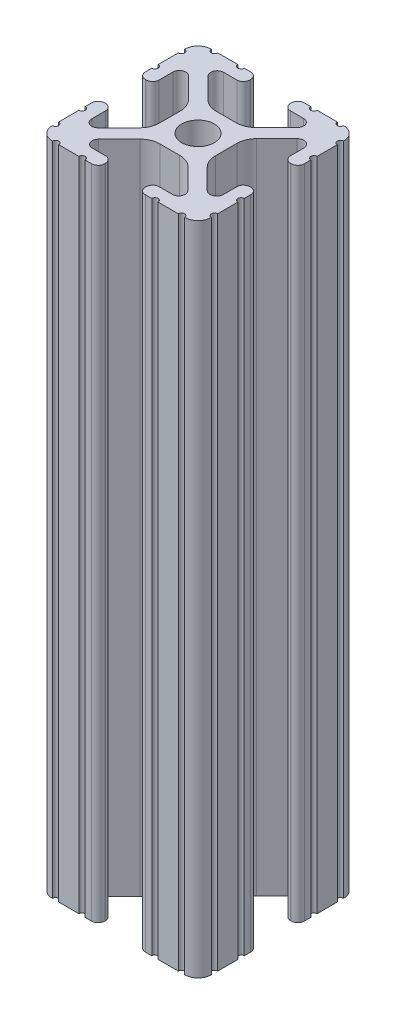
SolidWorks part; units mm, degrees
material "6061-T6 (SS)"
ref_plane "Front Plane" through (0, 0, 0) normal (0, 0, 1) x (1, 0, 0)
ref_plane "Top Plane" through (0, 0, 0) normal (0, 1, 0) x (1, 0, 0)
ref_plane "Right Plane" through (0, 0, 0) normal (1, 0, 0) x (0, 0, -1)
sketch "Sketch1" plane through (0, 0, 0) normal (0, 1, 0) x (0, 0, -1)
  line L0 (6.3331, -12.7) -> (9.5504, -12.7)
  line L1 (12.7, -9.5504) -> (12.7, -6.3331)
  line L2 (12.7, -5.3171) -> (12.7, -4.2875)
  line L3 (11.651, -3.2385) -> (11.5392, -3.2385)
  line L4 (10.4902, -4.2875) -> (10.4902, -6.4021)
  line L5 (8.7371, -7.1294) -> (5.441, -3.8408)
  line L6 (4.5085, -1.5932) -> (4.5085, 1.5932)
  line L7 (5.441, 3.8408) -> (8.7371, 7.1294)
  line L8 (10.4902, 6.4021) -> (10.4902, 4.2875)
  line L9 (11.5392, 3.2385) -> (11.651, 3.2385)
  line L10 (12.7, 4.2875) -> (12.7, 5.3171)
  line L11 (12.7, 6.3331) -> (12.7, 9.5504)
  line L12 (9.5504, 12.7) -> (6.3331, 12.7)
  line L13 (5.3171, 12.7) -> (4.2875, 12.7)
  line L14 (3.2385, 11.651) -> (3.2385, 11.5392)
  line L15 (4.2875, 10.4902) -> (6.4768, 10.4902)
  line L16 (7.207, 8.7244) -> (3.8983, 5.4232)
  line L17 (1.6558, 4.4958) -> (-1.6558, 4.4958)
  line L18 (-3.8983, 5.4232) -> (-7.207, 8.7244)
  line L19 (-6.4768, 10.4902) -> (-4.2875, 10.4902)
  line L20 (-3.2385, 11.5392) -> (-3.2385, 11.651)
  line L21 (-4.2875, 12.7) -> (-5.3171, 12.7)
  line L22 (-6.3331, 12.7) -> (-9.5504, 12.7)
  line L23 (-12.7, 9.5504) -> (-12.7, 6.3331)
  line L24 (-12.7, 5.3171) -> (-12.7, 4.2875)
  line L25 (-11.651, 3.2385) -> (-11.5392, 3.2385)
  line L26 (-10.4902, 4.2875) -> (-10.4902, 6.4021)
  line L27 (-8.7371, 7.1294) -> (-5.441, 3.8408)
  line L28 (-4.5085, 1.5932) -> (-4.5085, -1.5932)
  line L29 (-5.441, -3.8408) -> (-8.7371, -7.1294)
  line L30 (-10.4902, -6.4021) -> (-10.4902, -4.2875)
  line L31 (-11.5392, -3.2385) -> (-11.651, -3.2385)
  line L32 (-12.7, -4.2875) -> (-12.7, -5.3171)
  line L33 (-12.7, -6.3331) -> (-12.7, -9.5504)
  line L34 (-9.5504, -12.7) -> (-6.3331, -12.7)
  line L35 (-5.3171, -12.7) -> (-4.2875, -12.7)
  line L36 (-3.2385, -11.651) -> (-3.2385, -11.5392)
  line L37 (-4.2875, -10.4902) -> (-6.4164, -10.4902)
  line L38 (-7.1797, -8.6452) -> (-3.9523, -5.4237)
  line L39 (-1.7093, -4.4958) -> (1.7093, -4.4958)
  line L40 (3.9523, -5.4237) -> (7.1797, -8.6452)
  line L41 (6.4164, -10.4902) -> (4.2875, -10.4902)
  line L42 (3.2385, -11.5392) -> (3.2385, -11.651)
  line L43 (4.2875, -12.7) -> (5.3171, -12.7)
  circle A0 centre (0, 0) radius 2.6035
  arc A1 (6.3331, -12.7) -> (5.3171, -12.7) centre (5.8251, -12.7) ccw
  arc A2 (10.5664, -12.6998) -> (9.5504, -12.7) centre (10.0584, -12.7) ccw
  arc A3 (10.5664, -12.6998) -> (12.6998, -10.5664) centre (10.5918, -10.5918) ccw
  arc A4 (12.7, -9.5504) -> (12.6998, -10.5664) centre (12.7, -10.0584) ccw
  arc A5 (12.7, -5.3171) -> (12.7, -6.3331) centre (12.7, -5.8251) ccw
  arc A6 (12.7, -4.2875) -> (11.651, -3.2385) centre (11.651, -4.2875) ccw
  arc A7 (11.5392, -3.2385) -> (10.4902, -4.2875) centre (11.5392, -4.2875) ccw
  arc A8 (8.7371, -7.1294) -> (10.4902, -6.4021) centre (9.4628, -6.4021) ccw
  arc A9 (5.441, 3.8408) -> (4.5085, 1.5932) centre (7.6835, 1.5932) ccw
  arc A10 (10.4902, 6.4021) -> (8.7371, 7.1294) centre (9.4628, 6.4021) ccw
  arc A11 (10.4902, 4.2875) -> (11.5392, 3.2385) centre (11.5392, 4.2875) ccw
  arc A12 (11.651, 3.2385) -> (12.7, 4.2875) centre (11.651, 4.2875) ccw
  arc A13 (12.7, 6.3331) -> (12.7, 5.3171) centre (12.7, 5.8251) ccw
  arc A14 (12.6998, 10.5664) -> (12.7, 9.5504) centre (12.7, 10.0584) ccw
  arc A15 (12.6998, 10.5664) -> (10.5664, 12.6998) centre (10.5918, 10.5918) ccw
  arc A16 (9.5504, 12.7) -> (10.5664, 12.6998) centre (10.0584, 12.7) ccw
  arc A17 (5.3171, 12.7) -> (6.3331, 12.7) centre (5.8251, 12.7) ccw
  arc A18 (4.2875, 12.7) -> (3.2385, 11.651) centre (4.2875, 11.651) ccw
  arc A19 (3.2385, 11.5392) -> (4.2875, 10.4902) centre (4.2875, 11.5392) ccw
  arc A20 (7.207, 8.7244) -> (6.4768, 10.4902) centre (6.4768, 9.4563) ccw
  arc A21 (1.6558, 4.4958) -> (3.8983, 5.4232) centre (1.6558, 7.6708) ccw
  arc A22 (-3.8983, 5.4232) -> (-1.6558, 4.4958) centre (-1.6558, 7.6708) ccw
  arc A23 (-6.4768, 10.4902) -> (-7.207, 8.7244) centre (-6.4768, 9.4563) ccw
  arc A24 (-4.2875, 10.4902) -> (-3.2385, 11.5392) centre (-4.2875, 11.5392) ccw
  arc A25 (-3.2385, 11.651) -> (-4.2875, 12.7) centre (-4.2875, 11.651) ccw
  arc A26 (-6.3331, 12.7) -> (-5.3171, 12.7) centre (-5.8251, 12.7) ccw
  arc A27 (-10.5664, 12.6998) -> (-9.5504, 12.7) centre (-10.0584, 12.7) ccw
  arc A28 (-10.5664, 12.6998) -> (-12.6998, 10.5664) centre (-10.5918, 10.5918) ccw
  arc A29 (-12.7, 9.5504) -> (-12.6998, 10.5664) centre (-12.7, 10.0584) ccw
  arc A30 (-12.7, 5.3171) -> (-12.7, 6.3331) centre (-12.7, 5.8251) ccw
  arc A31 (-12.7, 4.2875) -> (-11.651, 3.2385) centre (-11.651, 4.2875) ccw
  arc A32 (-11.5392, 3.2385) -> (-10.4902, 4.2875) centre (-11.5392, 4.2875) ccw
  arc A33 (-8.7371, 7.1294) -> (-10.4902, 6.4021) centre (-9.4628, 6.4021) ccw
  arc A34 (-4.5085, 1.5932) -> (-5.441, 3.8408) centre (-7.6835, 1.5932) ccw
  arc A35 (-5.441, -3.8408) -> (-4.5085, -1.5932) centre (-7.6835, -1.5932) ccw
  arc A36 (-10.4902, -6.4021) -> (-8.7371, -7.1294) centre (-9.4628, -6.4021) ccw
  arc A37 (-10.4902, -4.2875) -> (-11.5392, -3.2385) centre (-11.5392, -4.2875) ccw
  arc A38 (-11.651, -3.2385) -> (-12.7, -4.2875) centre (-11.651, -4.2875) ccw
  arc A39 (-12.7, -6.3331) -> (-12.7, -5.3171) centre (-12.7, -5.8251) ccw
  arc A40 (-12.6998, -10.5664) -> (-12.7, -9.5504) centre (-12.7, -10.0584) ccw
  arc A41 (-12.6998, -10.5664) -> (-10.5664, -12.6998) centre (-10.5918, -10.5918) ccw
  arc A42 (-9.5504, -12.7) -> (-10.5664, -12.6998) centre (-10.0584, -12.7) ccw
  arc A43 (-5.3171, -12.7) -> (-6.3331, -12.7) centre (-5.8251, -12.7) ccw
  arc A44 (-4.2875, -12.7) -> (-3.2385, -11.651) centre (-4.2875, -11.651) ccw
  arc A45 (-3.2385, -11.5392) -> (-4.2875, -10.4902) centre (-4.2875, -11.5392) ccw
  arc A46 (-7.1797, -8.6452) -> (-6.4164, -10.4902) centre (-6.4164, -9.4098) ccw
  arc A47 (-1.7093, -4.4958) -> (-3.9523, -5.4237) centre (-1.7093, -7.6708) ccw
  arc A48 (3.9523, -5.4237) -> (1.7093, -4.4958) centre (1.7093, -7.6708) ccw
  arc A49 (6.4164, -10.4902) -> (7.1797, -8.6452) centre (6.4164, -9.4098) ccw
  arc A50 (4.2875, -10.4902) -> (3.2385, -11.5392) centre (4.2875, -11.5392) ccw
  arc A51 (3.2385, -11.651) -> (4.2875, -12.7) centre (4.2875, -11.651) ccw
  arc A52 (5.441, -3.8408) -> (4.5085, -1.5932) centre (7.6835, -1.5932) cw
  dimension "D1" = 3.175
extrude "Boss-Extrude1" add sketch "Sketch1" along normal blind 104.775
